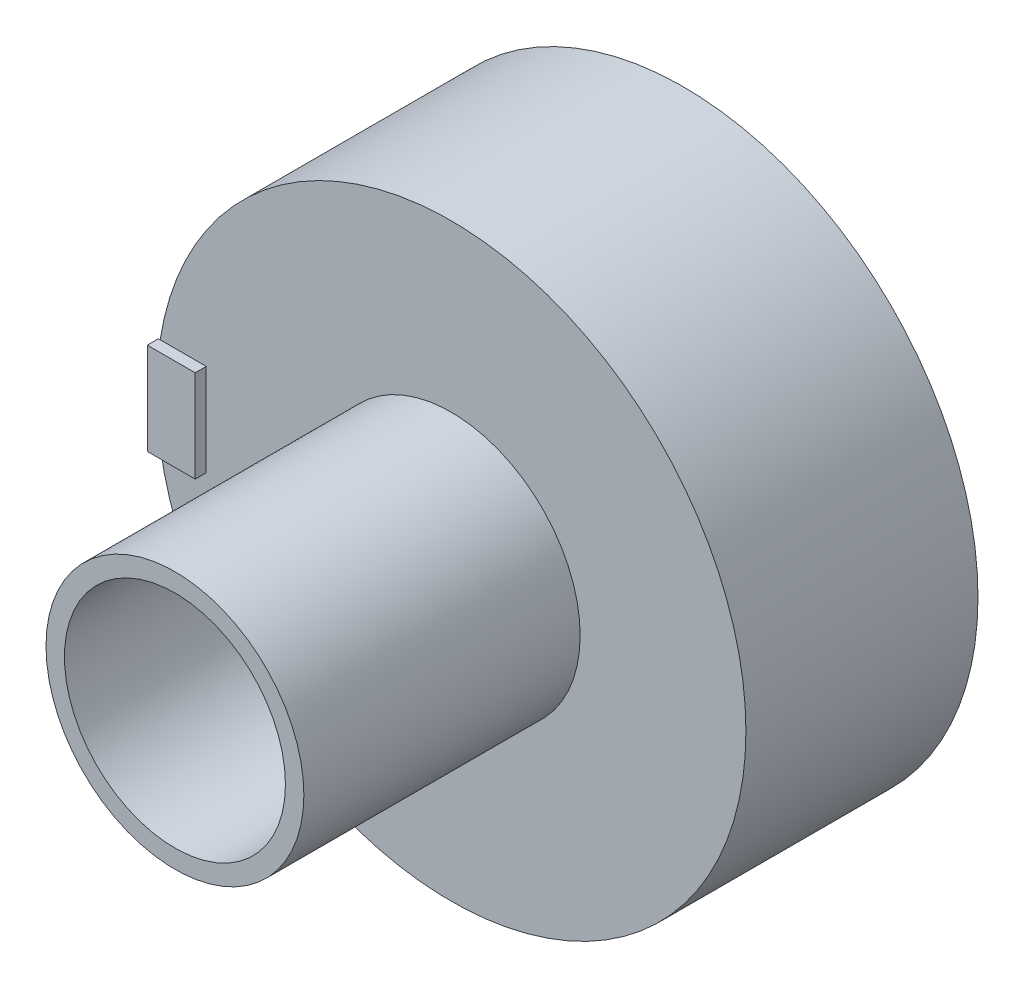
SolidWorks part; units mm, degrees
ref_plane "Front Plane" through (0, 0, 0) normal (0, 0, 1) x (1, 0, 0)
ref_plane "Top Plane" through (0, 0, 0) normal (0, 1, 0) x (1, 0, 0)
ref_plane "Right Plane" through (0, 0, 0) normal (1, 0, 0) x (0, 0, -1)
sketch "Sketch1" plane through (0, 0, 0) normal (0, 0, 1) x (1, 0, 0)
  circle A0 centre (0, 0) radius 8
  dimension "D1" = 16
extrude "Boss-Extrude1" add sketch "Sketch1" along normal blind 6.3
sketch "Sketch2" plane through (0, 0, 6.3) normal (0, 0, 1) x (1, 0, 0)
  circle A0 centre (0, 0) radius 3.5
  dimension "D1" = 7
extrude "Boss-Extrude2" add sketch "Sketch2" along normal blind 7.5
sketch "Sketch3" plane through (0, 0, 13.8) normal (0, 0, 1) x (1, 0, 0)
  circle A0 centre (0, 0) radius 3
  dimension "D1" = 6
extrude "Cut-Extrude1" cut sketch "Sketch3" against normal up to surface (7.5 mm away) up to face at (3.5, 0, 6.3)
sketch "Sketch4" plane through (0, 0, 6.3) normal (0, 0, 1) x (1, 0, 0)
  line L0 (0, 8) -> (0, -9.0943) construction
  line L2 (-11.0347, 0) -> (12.0906, 0) construction
  circle A0 centre (0, 0) radius 8 construction
sketch "Sketch5" plane through (0, 0, 6.3) normal (0, 0, 1) x (1, 0, 0)
  line L0 (-11.0347, 0) -> (12.0906, 0) construction
  line L1 (-7.95, 1.25) -> (-6.65, 1.25)
  line L2 (-7.95, 1.25) -> (-7.95, -1.25)
  line L3 (-7.95, -1.25) -> (-6.65, -1.25)
  line L4 (-6.65, 1.25) -> (-6.65, -1.25)
  line L5 (-7.3, 1.25) -> (-7.3, -1.25) construction
  dimension "D1" = 1.3
  dimension "D2" = 2.5
  dimension "D3" = 1.25
  dimension "D4" = 7.3
extrude "Boss-Extrude3" add sketch "Sketch5" along normal blind 0.3
